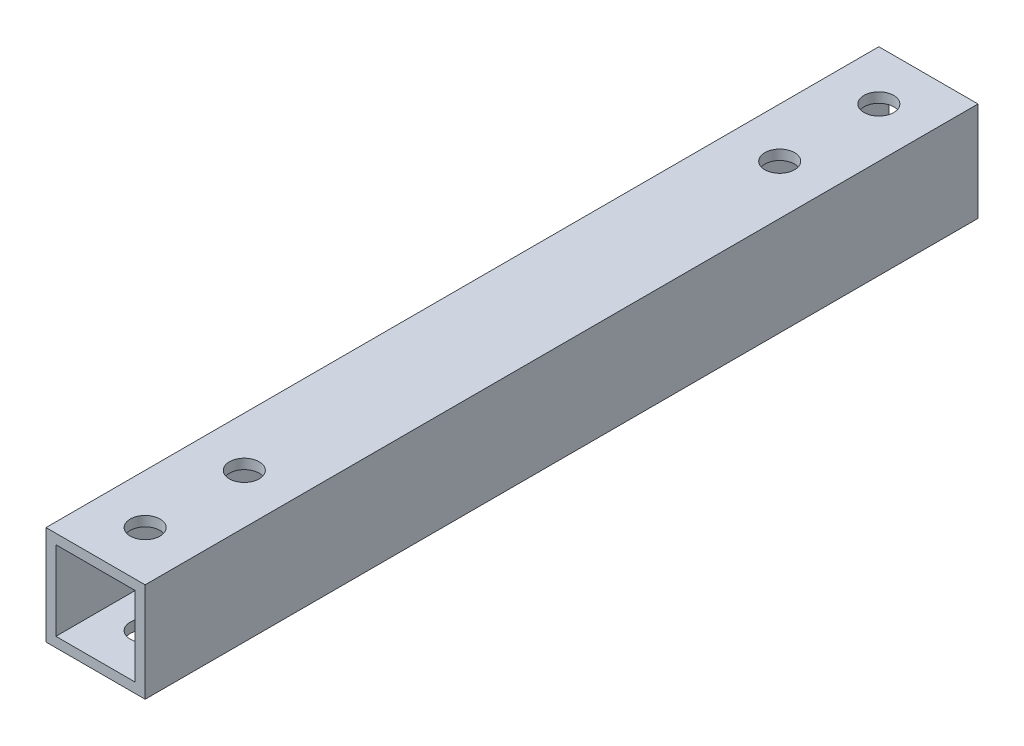
SolidWorks part; units mm, degrees
material "6063-O"
ref_plane "前视基准面" through (0, 0, 0) normal (0, 0, 1) x (1, 0, 0)
ref_plane "上视基准面" through (0, 0, 0) normal (0, 1, 0) x (1, 0, 0)
ref_plane "右视基准面" through (0, 0, 0) normal (1, 0, 0) x (0, 0, -1)
other "Configuration Table"
sketch "草图1" plane through (0, 0, 0) normal (0, 0, 1) x (1, 0, 0)
  line L1 (-77.0767, 0) -> (-67.0767, 0)
  line L2 (-77.0767, 0) -> (-77.0767, -10)
  line L3 (-77.0767, -10) -> (-67.0767, -10)
  line L4 (-67.0767, 0) -> (-67.0767, -10)
  line L5 (-77.0767, 0) -> (-67.0767, -10) construction
  line L6 (-77.0767, -10) -> (-67.0767, 0) construction
  point P4 (-72.0767, -5)
  dimension "D1" = 10
  dimension "D2" = 10
extrude "拉伸-薄壁1" add sketch "草图1" along normal blind 84 thin
sketch "草图3" plane through (0, -10, 0) normal (0, -1, 0) x (1, 0, 0)
  line L0 (-72.0767, 0) -> (-72.0767, 84) construction
  line L1 (-77.0767, 0) -> (-67.0767, 0) construction
  line L2 (-77.0767, 84) -> (-67.0767, 84) construction
  line L3 (-72.0767, 42) -> (-77.0767, 42) construction
  line L4 (-77.0767, 84) -> (-77.0767, 0) construction
  circle A0 centre (-72.0767, 5) radius 1.5
  circle A1 centre (-72.0767, 79) radius 1.5
  circle A2 centre (-72.0767, 69) radius 1.5
  circle A3 centre (-72.0767, 15) radius 1.5
  dimension "D1" = 3
  dimension "D2" = 5
  dimension "D3" = 10
extrude "切除-拉伸2" cut sketch "草图3" against normal blind 10
